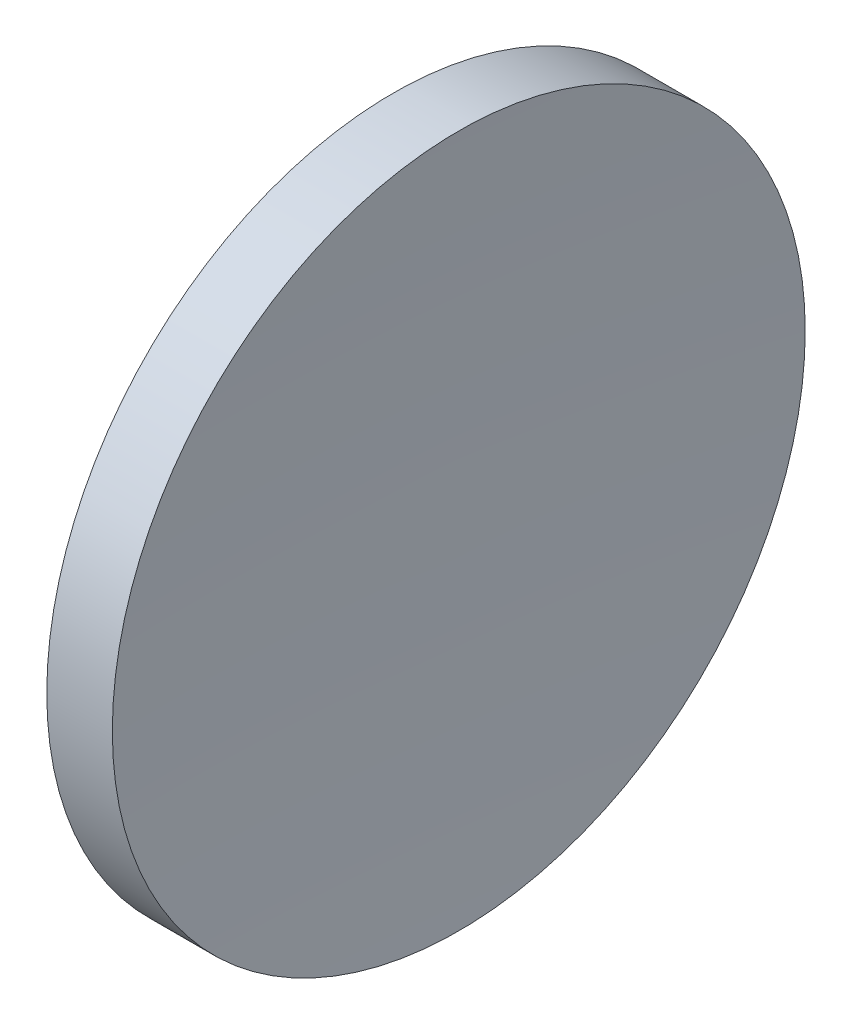
SolidWorks part; units mm, degrees
ref_plane "前视基准面" through (0, 0, 0) normal (0, 0, 1) x (1, 0, 0)
ref_plane "上视基准面" through (0, 0, 0) normal (0, 1, 0) x (1, 0, 0)
ref_plane "右视基准面" through (0, 0, 0) normal (1, 0, 0) x (0, 0, -1)
sketch "草图1" plane through (0, 0, 0) normal (0, 0, 1) x (1, 0, 0)
  line L0 (56.1009, 32.6108) -> (68.2773, 32.6108) construction
  line L1 (57.5323, 32.6108) -> (57.5323, 45.1108)
  line L2 (57.5323, 45.1108) -> (59.8975, 45.1108)
  line L3 (59.5323, 32.6108) -> (57.5323, 32.6108)
  arc A0 (59.8975, 45.1108) -> (59.5323, 32.6108) centre (265.6322, 32.8447) ccw
revolve "旋转1" add sketch "草图1" angle 360 about L0
